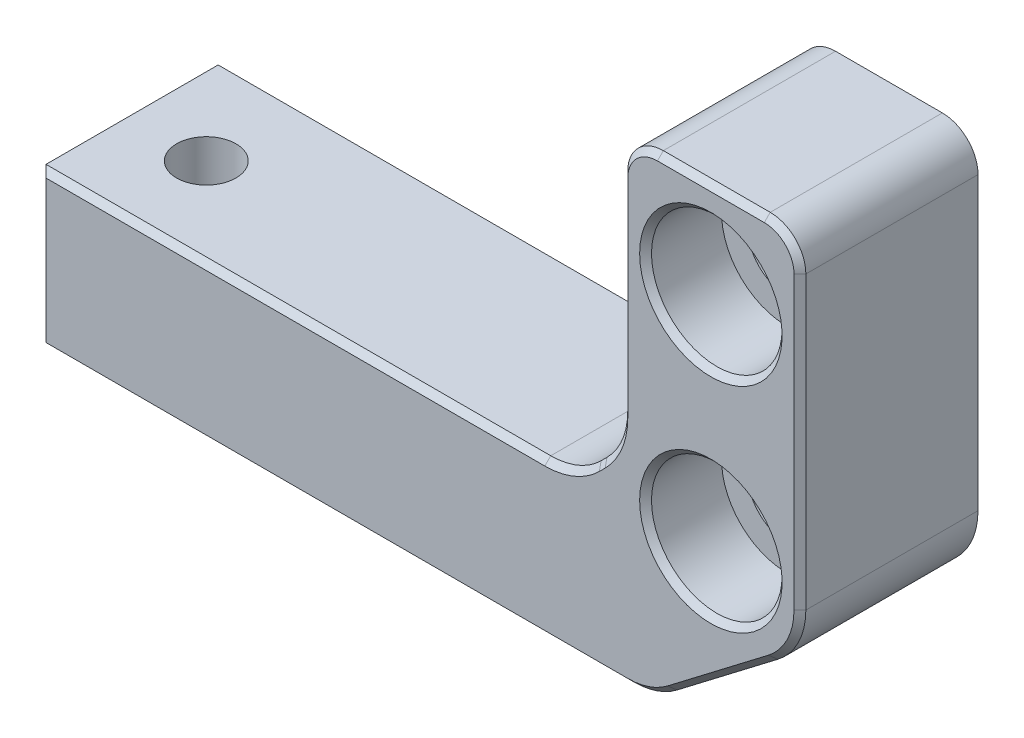
SolidWorks part; units mm, degrees
material "Alumina"
ref_plane "Plan de face" through (0, 0, 0) normal (0, 0, 1) x (1, 0, 0)
ref_plane "Plan de dessus" through (0, 0, 0) normal (0, 1, 0) x (1, 0, 0)
ref_plane "Plan de droite" through (0, 0, 0) normal (1, 0, 0) x (0, 0, -1)
sketch "Sketch1" plane through (0, 0, 0) normal (0, 0, 1) x (1, 0, 0)
  line L0 (26, 20.7005) -> (26, -11.3325) construction
  line L1 (22.6582, -18.5995) -> (31.1435, -12.1143)
  line L2 (16.2574, -5.0751) -> (16.7426, -4.5898)
  line L3 (-25, 4.1675) -> (-25, 20.7005) construction
  line L4 (-30.5, -6.8325) -> (12.0147, -6.8325)
  line L5 (-30.5, -6.8325) -> (-30.5, -19.8325)
  line L6 (-30.5, -19.8325) -> (19.0147, -19.8325)
  line L7 (33.5, -7.3472) -> (33.5, 17.1675)
  line L8 (30.5, 20.1675) -> (21.5, 20.1675)
  line L9 (18.5, -0.3472) -> (18.5, 17.1675)
  arc A0 (21.5, 20.1675) -> (18.5, 17.1675) centre (21.5, 17.1675) ccw
  arc A1 (33.5, 17.1675) -> (30.5, 20.1675) centre (30.5, 17.1675) ccw
  arc A2 (22.6582, -18.5995) -> (19.0147, -19.8325) centre (19.0147, -13.8325) cw
  arc A3 (31.1435, -12.1143) -> (33.5, -7.3472) centre (27.5, -7.3472) ccw
  arc A4 (16.2574, -5.0751) -> (12.0147, -6.8325) centre (12.0147, -0.8325) cw
  arc A5 (16.7426, -4.5898) -> (18.5, -0.3472) centre (12.5, -0.3472) ccw
  point P1 (33.5, -19.8325)
  point P7 (18.5, -6.8325)
  dimension "D2" = 3
  dimension "D3" = 6
  dimension "D1" = 5.5
  dimension "D4" = 40
  dimension "D5" = 13
  dimension "D6" = 15
  dimension "D7" = 7.5
extrude "Boss-Extrude1" add sketch "Sketch1" along normal blind 15
hole_wizard "CBORE for M6 Hex Socket Head Cap Screw1" positions "Sketch2" profile "Sketch3" counterbore size "M6" standard "ISO" end condition through all
sketch "Sketch2" plane through (0, 0, 15) normal (0, 0, 1) x (1, 0, 0)
  line L0 (30.5, 20.1675) -> (21.5, 20.1675) construction
  point P0 (26, 12.1675)
  point P2 (26, -5.8325)
  point P6 (26, 20.1675)
  dimension "D1" = 18
  dimension "D2" = 8
sketch "Sketch3" plane through (26, 12.1675, 15) normal (1, 0, 0) x (0, -1, 0)
  line L0 (0, 0) -> (0, 15)
  line L1 (0, 15) -> (3.3, 15)
  line L3 (3.3, 15) -> (3.3, 6.4)
  line L4 (3.3, 6.4) -> (5.5, 6.4)
  line L5 (5.5, 6.4) -> (5.5, 0)
  line L7 (5.5, 0) -> (0, 0)
  line L11 (0, -6.35) -> (0, 107.95) construction
  dimension "Thru Hole Dia." = 6.6
  dimension "Thru Hole Depth" = 15
  dimension "C'Bore Dia." = 11
  dimension "C'Bore Depth" = 6.4
hole_wizard "Tap Drill for M6 Tap1" positions "Sketch4" profile "Sketch5" hole size "M6" standard "ISO" end condition through all
sketch "Sketch4" plane through (0, -6.8325, 0) normal (0, 1, 0) x (1, 0, 0)
  line L0 (-30.5, -15) -> (-30.5, 0) construction
  point P0 (-24, -7.5)
  dimension "D1" = 6.5
sketch "Sketch5" plane through (-24, -6.8325, 7.5) normal (1, 0, 0) x (0, 0, 1)
  line L0 (0, 0) -> (0, 13)
  line L1 (0, 13) -> (2.5, 13)
  line L2 (2.5, 13) -> (2.5, 0)
  line L5 (2.5, 0) -> (0, 0)
  line L11 (0, -6.35) -> (0, 107.95) construction
  dimension "Thru Hole Dia." = 5
  dimension "Thru Hole Depth" = 13
chamfer "Chamfer1" distance 0.5 angle 45 16 edges at (31.5, 12.1675, 15) (31.5, -5.8325, 15) (-5.7426, -19.8325, 15) (20.9379, -19.5159, 15) (26.9008, -15.3569, 15) (32.8787, -10.006, 15) (33.5, 4.9102, 15) (32.6213, 19.2889, 15) (26, 20.1675, 15) (19.3787, 19.2889, 15) (18.5, 8.4102, 15) (18.0433, -2.6433, 15) (16.5, -4.8325, 15) (14.3108, -6.3757, 15) (-30.5, -13.3325, 15) (-9.2426, -6.8325, 15)
